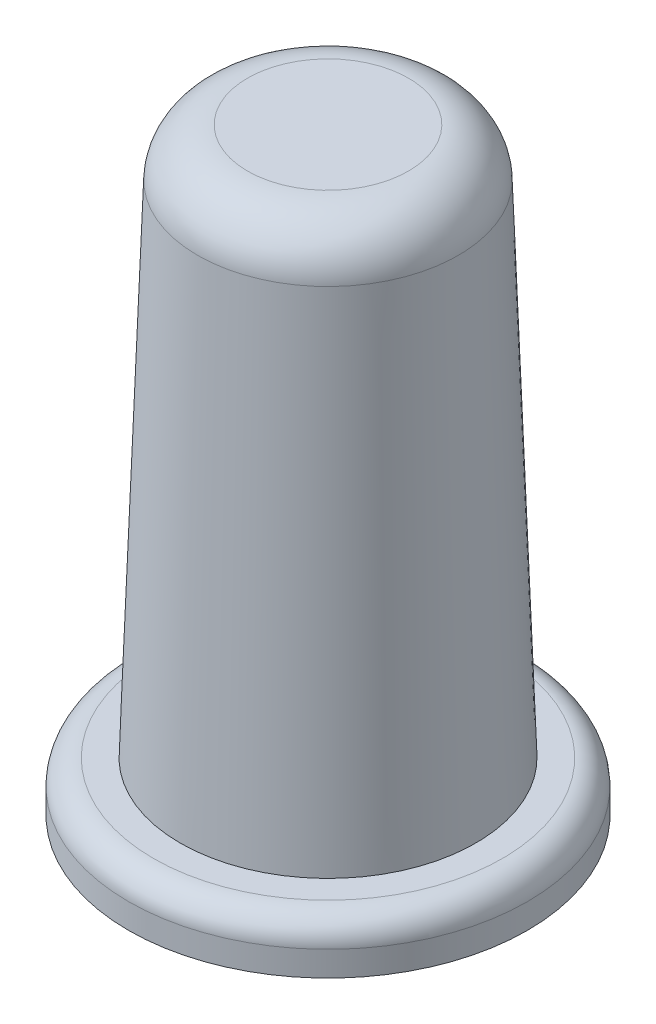
SolidWorks part; units mm, degrees
material "ABS"
ref_plane "Front Plane" through (0, 0, 0) normal (0, 0, 1) x (1, 0, 0)
ref_plane "Top Plane" through (0, 0, 0) normal (0, 1, 0) x (1, 0, 0)
ref_plane "Right Plane" through (0, 0, 0) normal (1, 0, 0) x (0, 0, -1)
sketch "Sketch1" plane through (0, 0, 0) normal (0, 1, 0) x (1, 0, 0)
  circle A0 centre (0, 0) radius 38.1
  dimension "D1" = 76.2
extrude "Boss-Extrude1" add sketch "Sketch1" along normal blind 152.4 draft 2
fillet "Fillet1" radius 12.7 1 edges at (0, 152.4, 32.7781)
sketch "Sketch2" plane through (0, 0, 0) normal (0, 1, 0) x (1, 0, 0)
  circle A0 centre (0, 0) radius 50.8
  dimension "D1" = 101.6
extrude "Boss-Extrude2" add sketch "Sketch2" along normal blind 12.7
fillet "Fillet2" radius 6.35 1 edges at (0, 12.7, 50.8)
